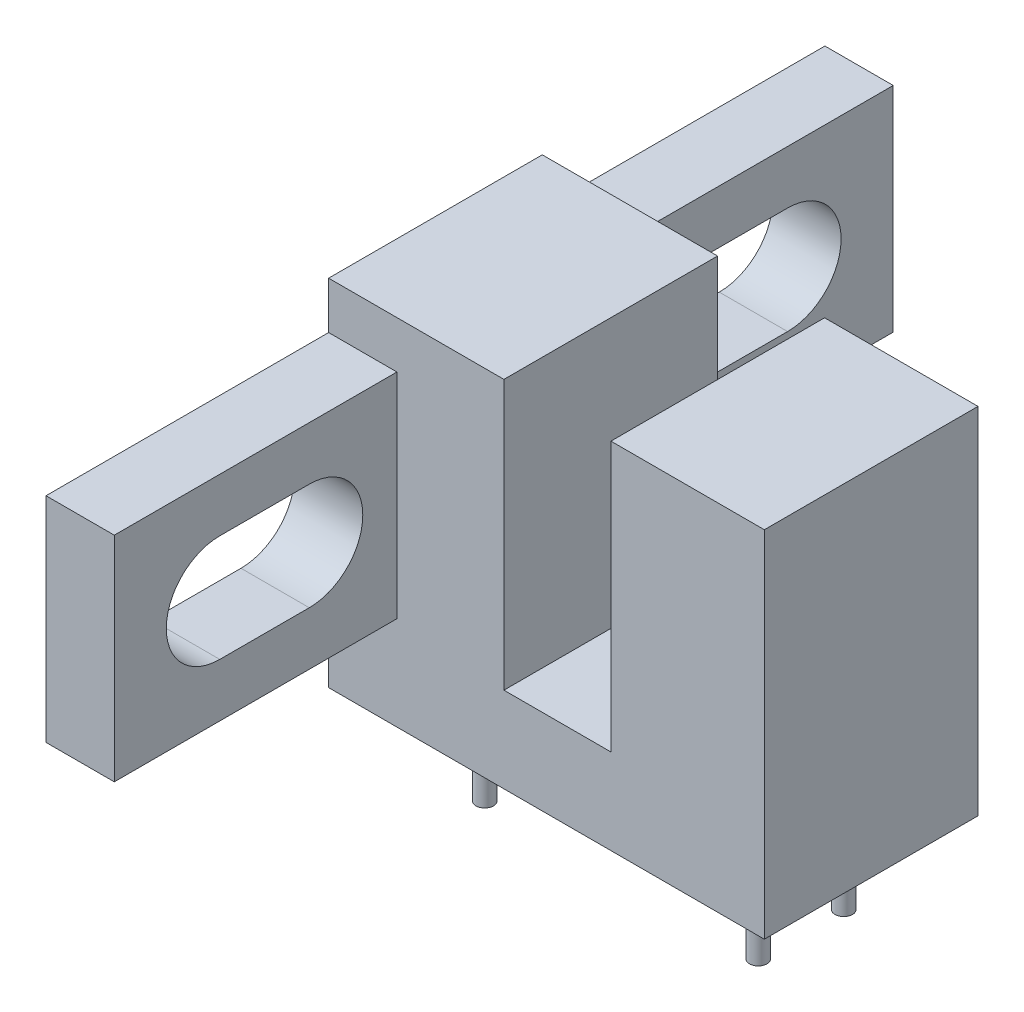
SolidWorks part; units mm, degrees
ref_plane "Front Plane" through (0, 0, 0) normal (0, 0, 1) x (1, 0, 0)
ref_plane "Top Plane" through (0, 0, 0) normal (0, 1, 0) x (1, 0, 0)
ref_plane "Right Plane" through (0, 0, 0) normal (1, 0, 0) x (0, 0, -1)
sketch "Sketch2" plane through (0, 0, 0) normal (0, 1, 0) x (1, 0, 0)
  line L7 (-6.475, -3.175) -> (6.475, -3.175)
  line L8 (-6.475, -3.175) -> (-6.475, 3.175)
  line L9 (-6.475, 3.175) -> (6.475, 3.175)
  line L10 (6.475, -3.175) -> (6.475, 3.175)
  line L11 (0, 3.175) -> (0, -3.175) construction
  line L12 (-6.475, 0) -> (6.475, 0) construction
extrude "Boss-Extrude1" add sketch "Sketch2" along normal blind 2.54 contours L7 L10 L9 L8
sketch "Sketch3" plane through (0, 2.54, 0) normal (0, 1, 0) x (1, 0, 0)
  line L1 (-6.475, -3.175) -> (6.475, -3.175) construction
  line L2 (6.475, -3.175) -> (6.475, 3.175) construction
  line L3 (-6.475, 3.175) -> (-1.265, 3.175)
  line L4 (-6.475, 3.175) -> (-6.475, -3.175)
  line L5 (-6.475, -3.175) -> (-1.265, -3.175)
  line L6 (-1.265, 3.175) -> (-1.265, -3.175)
  line L8 (6.475, 3.175) -> (1.915, 3.175)
  line L9 (6.475, 3.175) -> (6.475, -3.175)
  line L10 (6.475, -3.175) -> (1.915, -3.175)
  line L11 (1.915, 3.175) -> (1.915, -3.175)
extrude "Boss-Extrude2" add sketch "Sketch3" along normal blind 8 contours L6 L5 L4 L3 | L11 L10 L9 L8
sketch "Sketch5" plane through (0, 0, 0) normal (0, -1, 0) x (1, 0, 0)
  circle A0 centre (-3.74, -1.27) radius 0.26
  circle A1 centre (-3.74, 1.27) radius 0.26
  circle A2 centre (4.39, -1.27) radius 0.26
  circle A3 centre (4.39, 1.27) radius 0.26
extrude "Boss-Extrude5" add sketch "Sketch5" along normal blind 2.5
sketch "Sketch6" plane through (-6.475, 0, 0) normal (-1, 0, 0) x (0, 0, 1)
  line L0 (-8.4361, 7.555) -> (-5.7761, 7.555)
  line L1 (-8.4361, 4.375) -> (-5.7761, 4.375)
  line L2 (5.78, 7.555) -> (8.44, 7.555)
  line L3 (5.78, 4.375) -> (8.44, 4.375)
  line L8 (-11.575, 9.14) -> (11.575, 9.14)
  line L9 (-11.575, 9.14) -> (-11.575, 2.79)
  line L10 (-11.575, 2.79) -> (11.575, 2.79)
  line L11 (11.575, 9.14) -> (11.575, 2.79)
  circle A0 centre (-8.4361, 5.965) radius 1.59
  circle A1 centre (-5.7761, 5.965) radius 1.59
  circle A2 centre (5.78, 5.965) radius 1.59
  circle A3 centre (8.44, 5.965) radius 1.59
  line M18 (3.175, 0) -> (3.175, 10.54)
  line M20 (-3.175, 10.54) -> (-3.175, 0)
extrude "Boss-Extrude6" add sketch "Sketch6" against normal blind 2.03 contours L9 L10 L8 A1 L1 A0 L0 M20 | L11 L8 L10 A3 L3 A2 L2 M18
